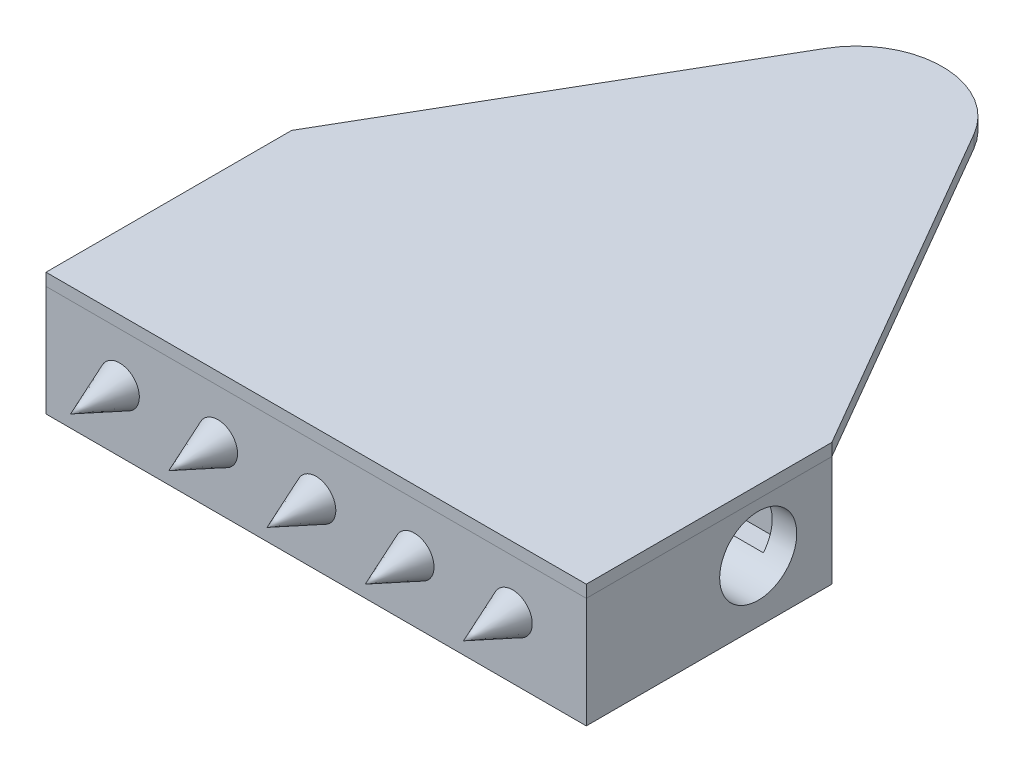
SolidWorks part; units mm, degrees
material "PLA/ABS"
ref_plane "Front Plane" through (0, 0, 0) normal (0, 0, 1) x (1, 0, 0)
ref_plane "Top Plane" through (0, 0, 0) normal (0, 1, 0) x (1, 0, 0)
ref_plane "Right Plane" through (0, 0, 0) normal (1, 0, 0) x (0, 0, -1)
other "Bounding Box"
ref_plane "Default Plane" through (-8.9266, -12.7485, 0) normal (-0.1736, 0.9848, 0) x (0.9848, 0.1736, 0)
sketch "Sketch1" plane through (0, 0, 0) normal (0, 1, 0) x (1, 0, 0)
  line L0 (0, 0) -> (0, -95.25) construction
  line L1 (0, -95.25) -> (-19.05, -95.25) construction
  line L2 (-76.2, -95.25) -> (-69.85, -95.25) construction
  line L3 (-69.85, -105.2195) -> (-19.05, -105.2195)
  line L4 (-69.85, -105.2195) -> (-69.85, -85.2805)
  line L5 (-69.85, -85.2805) -> (-19.05, -85.2805)
  line L6 (-19.05, -105.2195) -> (-19.05, -85.2805)
  line L7 (-69.85, -105.2195) -> (-19.05, -85.2805) construction
  line L8 (-69.85, -85.2805) -> (-19.05, -105.2195) construction
  line L9 (-88.9, -120.65) -> (-76.2, -120.65)
  line L10 (-88.9, -120.65) -> (-88.9, -69.85)
  line L11 (-88.9, -69.85) -> (-76.2, -69.85)
  line L12 (-76.2, -120.65) -> (-76.2, -69.85)
  line L13 (-88.9, -120.65) -> (-76.2, -69.85) construction
  line L14 (-88.9, -69.85) -> (-76.2, -120.65) construction
  line L15 (69.85, -85.2805) -> (19.05, -85.2805)
  line L16 (-63.5, -133.35) -> (-6.35, -133.35)
  line L17 (-63.5, -133.35) -> (-63.5, -116.84)
  line L18 (-63.5, -116.84) -> (-6.35, -116.84)
  line L19 (-6.35, -133.35) -> (-6.35, -116.84)
  line L20 (-63.5, -133.35) -> (-6.35, -116.84) construction
  line L21 (-63.5, -116.84) -> (-6.35, -133.35) construction
  line L22 (19.05, -105.2195) -> (19.05, -85.2805)
  line L23 (69.85, -105.2195) -> (19.05, -105.2195)
  line L24 (69.85, -105.2195) -> (69.85, -85.2805)
  line L25 (88.9, -69.85) -> (76.2, -69.85)
  line L26 (76.2, -120.65) -> (76.2, -69.85)
  line L27 (88.9, -120.65) -> (76.2, -120.65)
  line L28 (88.9, -120.65) -> (88.9, -69.85)
  line L30 (63.5, -133.35) -> (20.32, -133.35)
  line L31 (63.5, -133.35) -> (63.5, -113.2078)
  line L32 (63.5, -113.2078) -> (20.32, -113.2078)
  line L33 (20.32, -133.35) -> (20.32, -113.2078)
  line L34 (63.5, -133.35) -> (20.32, -113.2078) construction
  line L35 (63.5, -113.2078) -> (20.32, -133.35) construction
  line L36 (-69.85, -139.7) -> (69.85, -139.7)
  line L37 (-69.85, -139.7) -> (-69.85, -76.2)
  line L38 (-69.85, -76.2) -> (69.85, -76.2)
  line L39 (69.85, -139.7) -> (69.85, -76.2)
  line L40 (-69.85, -139.7) -> (69.85, -76.2) construction
  line L41 (-69.85, -76.2) -> (69.85, -139.7) construction
  circle A0 centre (0, 0) radius 69.85
  circle A1 centre (0, 0) radius 13.843
  point P3 (-34.925, -125.095)
  point P6 (-44.45, -95.25)
  point P12 (-82.55, -95.25)
  point P22 (0, -76.2)
  point P23 (0, -107.95)
  point P36 (0, -69.85)
  point P38 (41.91, -123.2789)
  dimension "D1" = 139.7
  dimension "D19" = 27.686
  dimension "D2" = 50.8
  dimension "D3" = 19.939
  dimension "D4" = 50.8
  dimension "D5" = 12.7
  dimension "D6" = 57.15
  dimension "D7" = 16.51
  dimension "D8" = 43.18
  dimension "D9" = 20.1422
  dimension "D10" = 6.35
  dimension "D11" = 139.7
  dimension "D12" = 44.45
  dimension "D13" = 6.35
  dimension "D14" = 6.35
  dimension "D15" = 6.35
  dimension "D16" = 6.35
  dimension "D17" = 63.5
  dimension "D18" = 6.35
sketch "Sketch2" plane through (0, 0, 0) normal (1, 0, 0) x (0, 0, -1)
  line L1 (-139.7, 12.7) -> (-76.2, 12.7)
  line L2 (-139.7, 12.7) -> (-139.7, -12.7)
  line L3 (-139.7, -12.7) -> (-76.2, -12.7)
  line L4 (-76.2, 12.7) -> (-76.2, -12.7)
  line L5 (-139.7, 12.7) -> (-76.2, -12.7) construction
  line L6 (-139.7, -12.7) -> (-76.2, 12.7) construction
  line L7 (-139.7, 12.7) -> (12.7, 12.7)
  line L8 (-139.7, 12.7) -> (-139.7, 15.875)
  line L9 (-139.7, 15.875) -> (12.7, 15.875)
  line L10 (12.7, 12.7) -> (12.7, 15.875)
  line L11 (-139.7, 12.7) -> (12.7, 15.875) construction
  line L12 (-139.7, 15.875) -> (12.7, 12.7) construction
  line L13 (-139.7, -12.7) -> (-76.2, -12.7)
  line L14 (-139.7, -12.7) -> (-139.7, -15.875)
  line L15 (-139.7, -15.875) -> (-76.2, -15.875)
  line L16 (-76.2, -12.7) -> (-76.2, -15.875)
  line L17 (-139.7, -12.7) -> (-76.2, -15.875) construction
  line L18 (-139.7, -15.875) -> (-76.2, -12.7) construction
  circle A0 centre (-95.25, 0) radius 25.4
  point P4 (-120.65, 0)
  point P5 (-107.95, 0)
  point P15 (-63.5, 14.2875)
  point P19 (-107.95, -14.2875)
  dimension "D1" = 25.4
  dimension "D2" = 3.175
  dimension "D3" = 12.7
sketch "Sketch3" plane through (0, 0, 0) normal (0, 1, 0) x (1, 0, 0)
  line L1 (-69.85, -139.7) -> (69.85, -139.7)
  line L2 (-69.85, -139.7) -> (-69.85, -76.2)
  line L3 (-69.85, -76.2) -> (69.85, -76.2)
  line L4 (69.85, -139.7) -> (69.85, -76.2)
  line L5 (-69.85, -139.7) -> (69.85, -76.2) construction
  line L6 (-69.85, -76.2) -> (69.85, -139.7) construction
  line L7 (-63.5, -82.55) -> (63.5, -82.55)
  line L8 (-63.5, -82.55) -> (-63.5, -133.35)
  line L9 (-63.5, -133.35) -> (63.5, -133.35)
  line L10 (63.5, -82.55) -> (63.5, -133.35)
  line L11 (-63.5, -82.55) -> (63.5, -133.35) construction
  line L12 (-63.5, -133.35) -> (63.5, -82.55) construction
  point P0 (0, -107.95)
  point P7 (0, -107.95)
extrude "Boss-Extrude1" add sketch "Sketch3" along normal up to vertex (12.7 mm away) and the other way up to vertex (12.7 mm away) up to point (0, 12.7, 139.7) other way up to point (0, -12.7, 139.7)
sketch "Sketch4" plane through (0, -12.7, 0) normal (0, -1, 0) x (1, 0, 0)
  line L1 (-69.85, 139.7) -> (69.85, 139.7)
  line L2 (-69.85, 139.7) -> (-69.85, 76.2)
  line L3 (-69.85, 76.2) -> (69.85, 76.2)
  line L4 (69.85, 139.7) -> (69.85, 76.2)
  line L5 (-69.85, 139.7) -> (69.85, 76.2) construction
  line L6 (-69.85, 76.2) -> (69.85, 139.7) construction
  point P0 (0, 107.95)
extrude "Boss-Extrude2" add sketch "Sketch4" along normal up to vertex (3.175 mm away) up to point (0, -15.875, 139.7)
sketch "Sketch5" plane through (0, 12.7, 0) normal (0, 1, 0) x (1, 0, 0)
  line L0 (-19.229, 11.1443) -> (-69.85, -76.2)
  line L1 (-69.85, -76.2) -> (-69.85, -139.7)
  line L2 (-69.85, -139.7) -> (69.85, -139.7)
  line L3 (69.85, -139.7) -> (69.85, -76.2)
  line L4 (69.85, -76.2) -> (19.229, 11.1443)
  arc A0 (-19.229, 11.1443) -> (19.229, 11.1443) centre (0, 0) cw
  dimension "D1" = 22.225
extrude "Boss-Extrude3" add sketch "Sketch5" along normal up to vertex (3.175 mm away) separate body up to point (0, 15.875, 139.7)
sketch "Sketch7" plane through (0, -12.7, 0) normal (0, 1, 0) x (1, 0, 0)
  line L0 (-19.05, -105.2195) -> (-19.05, -85.2805) construction
  line L1 (-63.5, -82.55) -> (-19.05, -82.55)
  line L2 (-63.5, -82.55) -> (-63.5, -107.95)
  line L3 (-63.5, -107.95) -> (-19.05, -107.95)
  line L4 (-19.05, -82.55) -> (-19.05, -107.95)
  line L5 (-63.5, -82.55) -> (-19.05, -107.95) construction
  line L6 (-63.5, -107.95) -> (-19.05, -82.55) construction
  line L7 (63.5, -82.55) -> (19.05, -82.55)
  line L8 (63.5, -82.55) -> (63.5, -107.95)
  line L9 (63.5, -107.95) -> (19.05, -107.95)
  line L10 (19.05, -82.55) -> (19.05, -107.95)
  line L11 (63.5, -82.55) -> (19.05, -107.95) construction
  line L12 (63.5, -107.95) -> (19.05, -82.55) construction
  line L13 (19.05, -105.2195) -> (19.05, -85.2805) construction
  line L14 (0, -95.25) -> (-19.05, -95.25) construction
  point P4 (-41.275, -95.25)
  point P10 (41.275, -95.25)
extrude "Boss-Extrude4" add sketch "Sketch7" along normal blind 6.35
sketch "Sketch6" plane through (-69.85, 0, 0) normal (-1, 0, 0) x (0, 0, 1)
  circle A0 centre (95.25, 0) radius 9.9695
extrude "Cut-Extrude1" cut sketch "Sketch6" against normal through all
ref_plane "Plane1" through (0, 0, 0) normal (1, 0, 0) x (0, 0, -1)
sketch "Sketch9" plane through (0, 0, 0) normal (1, 0, 0) x (0, 0, -1)
  line L0 (-139.7, 0) -> (-139.7, 5.08)
  line L1 (-139.7, 12.7) -> (-139.7, -15.875) construction
  line L2 (-139.7, 5.08) -> (-152.4, 0)
  line L3 (-152.4, 0) -> (-139.7, 0)
  dimension "D1" = 12.7
  dimension "D2" = 5.08
revolve "Revolve1" add sketch "Sketch9" angle 360 about L3
pattern_linear "LPattern1" count 3 spacing 25.4 along (-1, 0, 0) count 3 spacing 25.4 along (1, 0, 0) of "Revolve1"
